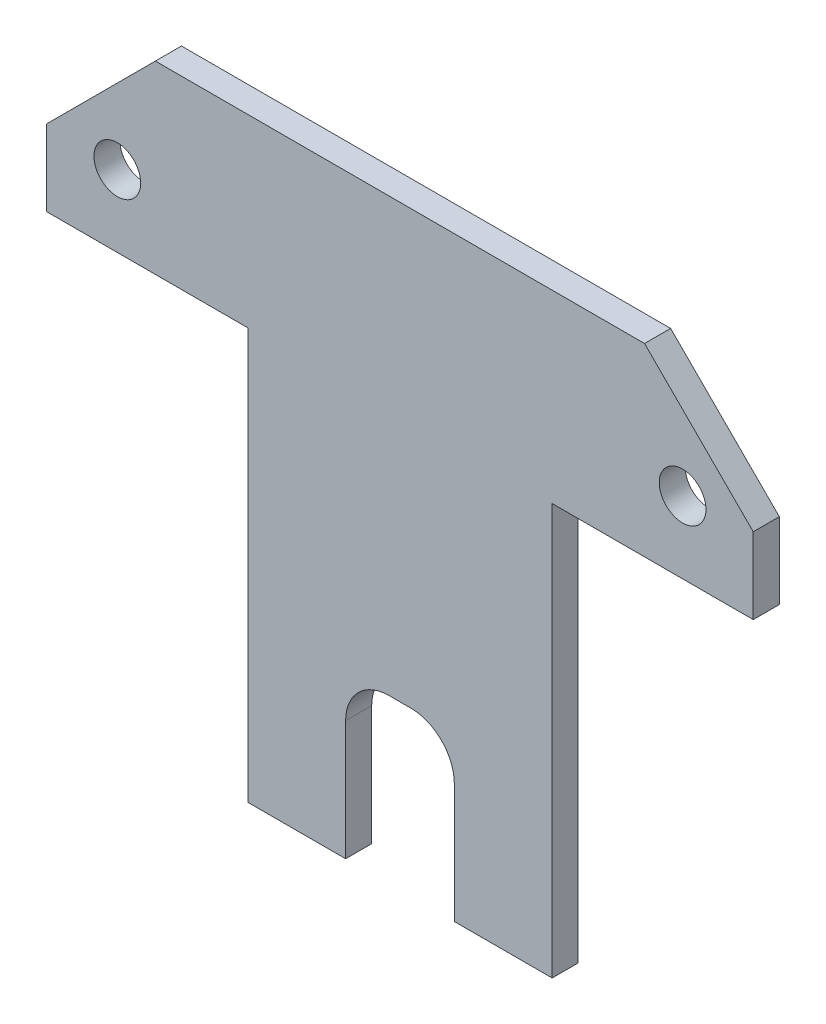
SolidWorks part; units mm, degrees
ref_plane "Спереди" through (0, 0, 0) normal (0, 0, 1) x (1, 0, 0)
ref_plane "Сверху" through (0, 0, 0) normal (0, 1, 0) x (1, 0, 0)
ref_plane "Справа" through (0, 0, 0) normal (1, 0, 0) x (0, 0, -1)
sketch "Sketch1" plane through (0, 0, 0) normal (0, 0, 1) x (1, 0, 0)
  line L0 (-21.1056, 33.0747) -> (23.8944, 33.0747)
  line L1 (23.8944, 33.0747) -> (33.8944, 23.0747)
  line L2 (33.8944, 23.0747) -> (33.8944, 16.0747)
  line L3 (33.8944, 16.0747) -> (15.3944, 16.0747)
  line L4 (15.3944, 16.0747) -> (15.3944, -21.7253)
  line L5 (15.3944, -21.7253) -> (-12.6056, -21.7253)
  line L6 (-12.6056, -21.7253) -> (-12.6056, 16.0747)
  line L7 (-12.6056, 16.0747) -> (-31.1056, 16.0747)
  line L8 (-31.1056, 16.0747) -> (-31.1056, 23.0747)
  line L9 (-31.1056, 23.0747) -> (-21.1056, 33.0747)
  line L10 (-31.5056, 22.6747) -> (34.2944, 22.6747) construction
  line L11 (-31.1056, 21.0747) -> (33.8944, 21.0747) construction
  circle A0 centre (-24.6056, 22.6747) radius 2.15
  circle A1 centre (27.3944, 22.6747) radius 2.15
  point P16 (1.3944, 22.6747)
  dimension "D5" = 52
  dimension "D8" = 4.3
  dimension "D9" = 28
  dimension "D1" = 65
  dimension "D2" = 45
  dimension "D3" = 10
  dimension "D4" = 17
  dimension "D6" = 10.4
  dimension "D7" = 26
  dimension "D10" = 12
  dimension "D11" = 42.8
extrude "Boss-Extrude1" add sketch "Sketch1" along normal blind 2.4
sketch "Sketch2" plane through (0, 0, 2.4) normal (0, 0, 1) x (1, 0, 0)
  line L0 (1.3944, 33.0747) -> (1.3944, -21.7253) construction
  line L1 (23.8944, 33.0747) -> (-21.1056, 33.0747) construction
  line L2 (-12.6056, -21.7253) -> (15.3944, -21.7253) construction
  line L4 (6.3944, -36.7253) -> (-3.6056, -36.7253)
  line L5 (6.3944, -36.7253) -> (6.3944, -6.7253)
  line L6 (6.3944, -6.7253) -> (-3.6056, -6.7253)
  line L7 (-3.6056, -36.7253) -> (-3.6056, -6.7253)
  line L8 (6.3944, -36.7253) -> (-3.6056, -6.7253) construction
  line L9 (6.3944, -6.7253) -> (-3.6056, -36.7253) construction
  dimension "D1" = 10
  dimension "D2" = 15
extrude "Cut-Extrude1" cut sketch "Sketch2" against normal through all
fillet "Fillet1" radius 4 2 edges at (6.3944, -6.7253, 1.2) (-3.6056, -6.7253, 1.2)
